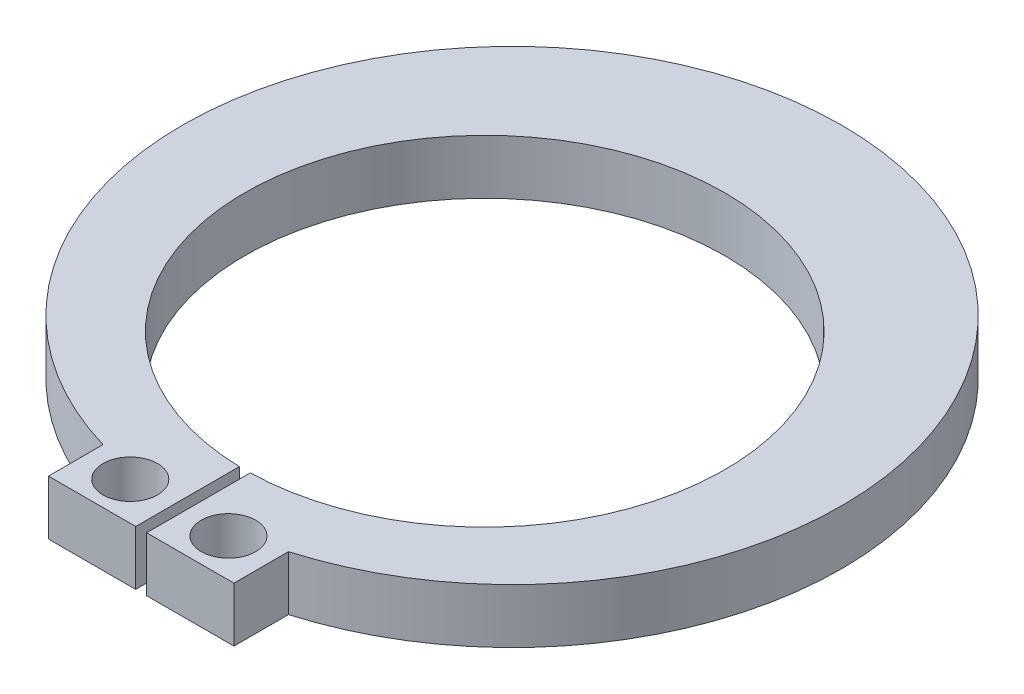
SolidWorks part; units mm, degrees
ref_plane "Front Plane" through (0, 0, 0) normal (0, 0, 1) x (1, 0, 0)
ref_plane "Top Plane" through (0, 0, 0) normal (0, 1, 0) x (1, 0, 0)
ref_plane "Right Plane" through (0, 0, 0) normal (1, 0, 0) x (0, 0, -1)
sketch "Sketch1" plane through (0, 0, 0) normal (0, 1, 0) x (1, 0, 0)
  line L0 (0, -55) -> (0, 55) construction
  line L1 (-55, 0) -> (55, 0) construction
  line L2 (-1.7, -6.8) -> (-0.1, -6.8)
  line L3 (-0.1, -6.8) -> (-0.1, -4.8989)
  line L4 (0.1, -6.8) -> (0.1, -4.8989)
  line L5 (-1.7, -6.8) -> (-1.7, -5.8)
  line L6 (1.7, -6.8) -> (1.7, -5.8)
  line L7 (0.1, -6.8) -> (1.7, -6.8)
  line L8 (0, -7.3817) -> (0, 10.8046) construction
  arc A1 (0.1, -4.8989) -> (-0.1, -4.8989) centre (0, -0.5) ccw
  arc A2 (1.7, -5.8) -> (-1.7, -5.8) centre (0, 0) ccw
  circle A3 centre (-0.9, -6.1) radius 0.5
  circle A4 centre (0.9, -6.1) radius 0.5
  dimension "D1" = 0.5
  dimension "D2" = 6.3
  dimension "D7" = 0.8
  dimension "D10" = 4.4
  dimension "D3" = 3.4
  dimension "D4" = 1.7
  dimension "D5" = 0.2
  dimension "D6" = 0.1
  dimension "D8" = 0.7
  dimension "D9" = 1
extrude "Boss-Extrude1" add sketch "Sketch1" along normal blind 1
